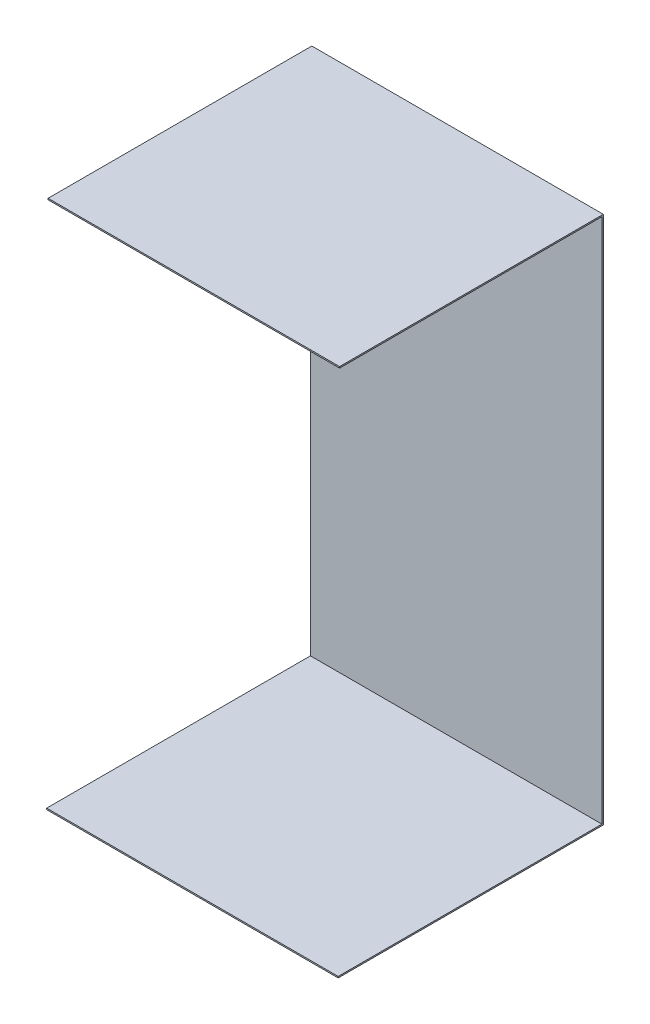
SolidWorks part; units mm, degrees
ref_plane "Front Plane" through (0, 0, 0) normal (0, 0, 1) x (1, 0, 0)
ref_plane "Top Plane" through (0, 0, 0) normal (0, 1, 0) x (1, 0, 0)
ref_plane "Right Plane" through (0, 0, 0) normal (1, 0, 0) x (0, 0, -1)
sketch "Sketch3" plane through (0, 0, 0) normal (0, 0, 1) x (1, 0, 0)
  line L1 (0, 0) -> (420, 0)
  line L2 (0, 0) -> (0, 760)
  line L3 (0, 760) -> (420, 760)
  line L4 (420, 0) -> (420, 760)
extrude "Boss-Extrude1" add sketch "Sketch3" along normal blind 2
ref_plane "Plane2" through (420, 760, 0) normal (-1, 0, 0) x (0, 0, 1)
sketch "Sketch7" plane through (420, 760, 0) normal (-1, 0, 0) x (0, 0, 1)
  line L1 (0, 0) -> (380, 0)
  line L2 (0, 0) -> (0, 2)
  line L3 (0, 2) -> (380, 2)
  line L4 (380, 0) -> (380, 2)
extrude "Boss-Extrude2" add sketch "Sketch7" along normal blind 420
ref_plane "Plane4" through (420, 0, 2) normal (1, 0, 0) x (0, 0, -1)
sketch "Sketch9" plane through (420, 0, 2) normal (1, 0, 0) x (0, 0, -1)
  line L1 (2, 0) -> (-380, 0)
  line L2 (2, 0) -> (2, 2)
  line L3 (2, 2) -> (-380, 2)
  line L4 (-380, 0) -> (-380, 2)
extrude "Boss-Extrude3" add sketch "Sketch9" against normal blind 420
